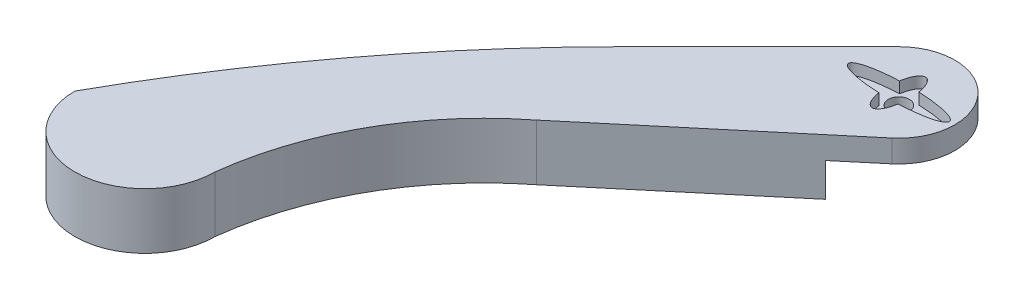
SolidWorks part; units mm, degrees
ref_plane "前视基准面" through (0, 0, 0) normal (0, 0, 1) x (1, 0, 0)
ref_plane "上视基准面" through (0, 0, 0) normal (0, 1, 0) x (1, 0, 0)
ref_plane "右视基准面" through (0, 0, 0) normal (1, 0, 0) x (0, 0, -1)
sketch "草图1" plane through (0, 0, 0) normal (0, 1, 0) x (1, 0, 0)
  line L0 (-14.1421, 14.1421) -> (-63.6396, -35.3553)
  line L1 (12.8558, -15.3209) -> (-56.0882, -73.1718)
  line L3 (-63.6396, -35.3553) -> (-56.0882, -73.1718) construction
  arc A0 (12.8558, -15.3209) -> (-14.1421, 14.1421) centre (0, 0) ccw
  arc A1 (-147.4785, -146.6526) -> (-97.4785, -146.6526) centre (-122.4785, -146.6526) ccw
  arc A2 (-56.0882, -73.1718) -> (-97.4785, -146.6526) centre (11.7362, -159.7734) ccw
  arc A3 (-63.6396, -35.3553) -> (-147.4785, -146.6526) centre (289.9138, -388.9087) ccw
  dimension "D1" = 40
  dimension "D2" = 50
  dimension "D5" = 110
  dimension "D6" = 500
  dimension "D3" = 90
  dimension "D4" = 70
  dimension "D7" = 146.6526
extrude "凸台-拉伸1" add sketch "草图1" along normal mid plane 20 contours A3 A1 A2 L1 A0 L0
ref_plane "基准面1" through (0, 10, 0) normal (0, -1, 0) x (-1, 0, 0)
sketch "草图2" plane through (0, 10, 0) normal (0, -1, 0) x (-1, 0, 0)
  circle A0 centre (0, 0) radius 3.75
sketch "草图3" plane through (0, 10, 0) normal (0, -1, 0) x (-1, 0, 0)
  line L0 (0, 0) -> (18, 0) construction
  line L1 (0, 0) -> (0, 9.5) construction
  ellipse E0 centre (0, 0) end of major axis (18, 0) minor radius 3.75 (-3.4572, 3.6802) -> (-3.4572, -3.6802) ccw
  ellipse E1 centre (0, 0) end of major axis (0, 9.5) minor radius 3.75 (-3.4572, -3.6802) -> (3.4572, -3.6802) ccw
  ellipse E2 centre (0, 0) end of major axis (0, 9.5) minor radius 3.75 (3.4572, 3.6802) -> (-3.4572, 3.6802) ccw
  ellipse E3 centre (0, 0) end of major axis (18, 0) minor radius 3.75 (3.4572, -3.6802) -> (3.4572, 3.6802) ccw
extrude "切除-拉伸2" cut sketch "草图2" against normal through all and the other way through all
extrude "切除-拉伸3" cut sketch "草图3" against normal blind 4 and the other way blind 4
ref_plane "基准面2" through (0, -10, 0) normal (0, -1, 0) x (-1, 0, 0)
sketch "草图4" plane through (0, -10, 0) normal (0, -1, 0) x (-1, 0, 0)
  line L1 (-12.8558, -15.3209) -> (56.0882, -73.1718) construction
  line L2 (0, -26.1081) -> (54.7968, -26.5125)
  line L3 (14.1421, 14.1421) -> (63.6396, -35.3553) construction
  line L4 (54.7968, -26.5125) -> (14.7725, 13.5118)
  line L5 (0, -26.1081) -> (-12.8558, -15.3209)
  arc A4 (14.7725, 13.5118) -> (-12.8558, -15.3209) centre (0.0064, 0.0076) ccw
extrude "切除-拉伸4" cut sketch "草图4" against normal blind 12 contours A4 L5 L2 L4
